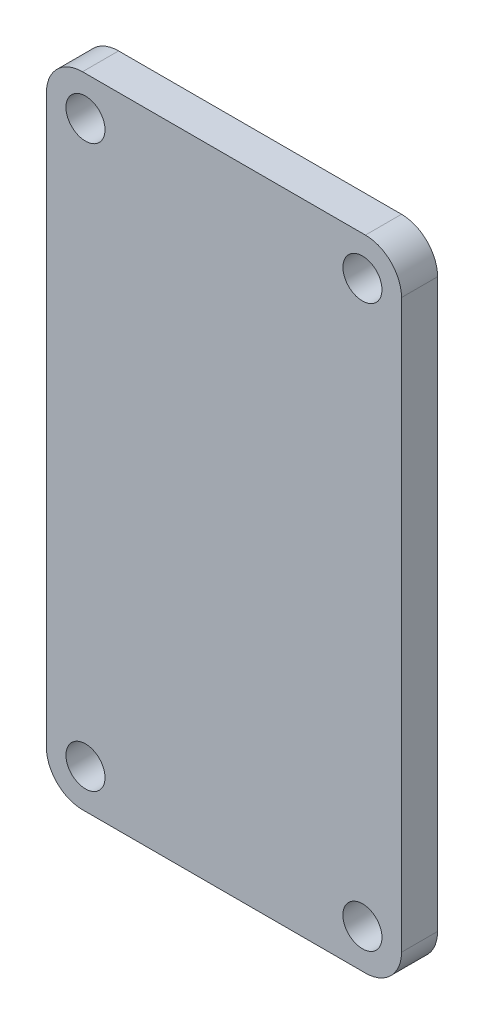
SolidWorks part; units mm, degrees
ref_plane "Front Plane" through (0, 0, 0) normal (0, 0, 1) x (1, 0, 0)
ref_plane "Top Plane" through (0, 0, 0) normal (0, 1, 0) x (1, 0, 0)
ref_plane "Right Plane" through (0, 0, 0) normal (1, 0, 0) x (0, 0, -1)
sketch "Sketch1" plane through (0, 0, 0) normal (0, 0, 1) x (1, 0, 0)
  line L0 (12.5, 0) -> (12.5, -45) construction
  line L1 (0, 0) -> (25, 0)
  line L2 (0, 0) -> (0, -45)
  line L3 (0, -45) -> (25, -45)
  line L4 (25, 0) -> (25, -45)
  line L5 (0, -22.5) -> (25, -22.5) construction
  circle A0 centre (2.75, -2.75) radius 1.375
  circle A1 centre (2.75, -42.25) radius 1.375
  circle A2 centre (22.25, -42.25) radius 1.375
  circle A3 centre (22.25, -2.75) radius 1.375
  dimension "D3" = 2.75
  dimension "D1" = 25
  dimension "D2" = 45
  dimension "D4" = 19.5
  dimension "D5" = 39.5
extrude "Boss-Extrude1" add sketch "Sketch1" along normal blind 2.54
fillet "Fillet1" radius 2.54 4 edges at (25, 0, 1.27) (25, -45, 1.27) (0, -45, 1.27) (0, 0, 1.27)
